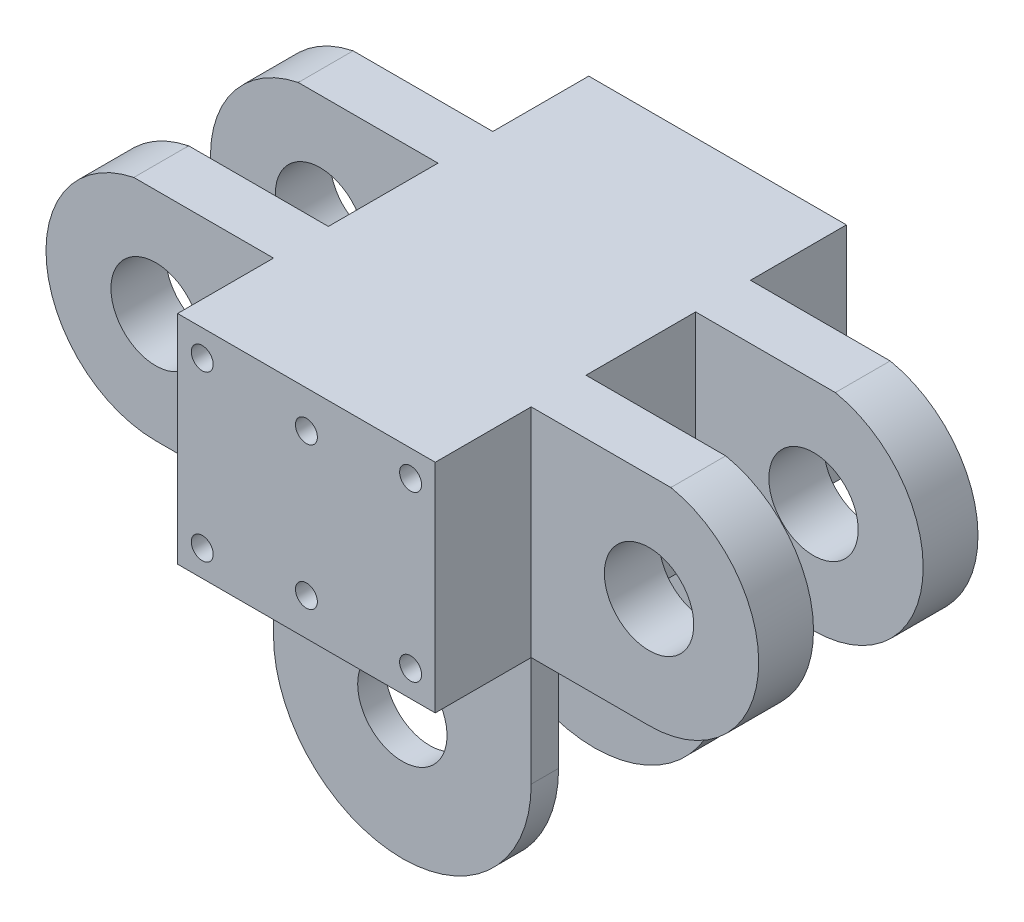
SolidWorks part; units mm, degrees
ref_plane "Płaszczyzna przednia" through (0, 0, 0) normal (0, 0, 1) x (1, 0, 0)
ref_plane "Płaszczyzna górna" through (0, 0, 0) normal (0, 1, 0) x (1, 0, 0)
ref_plane "Płaszczyzna prawa" through (0, 0, 0) normal (1, 0, 0) x (0, 0, -1)
sketch "Szkic1" plane through (0, 0, 0) normal (0, 0, 1) x (1, 0, 0)
  line L8 (47, 19.8) -> (0, 19.8) construction
  line L11 (0, 0) -> (47, 0)
  line L12 (0, 0) -> (0, 39.6)
  line L13 (0, 39.6) -> (47, 39.6)
  line L14 (47, 0) -> (47, 39.6)
  dimension "D1" = 39.6
  dimension "D4" = 47
extrude "Dodanie-wyciągnięcie3" add sketch "Szkic1" along normal blind 75
ref_plane "Płaszczyzna1" through (0, 0, 37.5) normal (0, 0, -1) x (-1, 0, 0)
ref_plane "Płaszczyzna2" through (0, 0, 27.5) normal (0, 0, -1) x (-1, 0, 0)
sketch "Szkic4" plane through (0, 0, 27.5) normal (0, 0, -1) x (-1, 0, 0)
  line L0 (-47, 39.6) -> (-72.4799, 39.6)
  line L2 (-68.5, 0) -> (-47, 0)
  line L3 (-47, 39.6) -> (0, 39.6) construction
  line L5 (-23.5, 39.6) -> (-23.5, 0) construction
  line L10 (-47, 39.6) -> (-47, 0)
  line L11 (-47, 0) -> (0, 0) construction
  line L12 (21.5, 0) -> (0, 0)
  line L13 (0, 39.6) -> (0, 0)
  line L14 (0, 39.6) -> (25.4799, 39.6)
  arc A4 (-72.4799, 39.6) -> (-68.5, 0) centre (-68.5, 20) ccw
  circle A5 centre (-68.5, 20) radius 8.15
  arc A6 (25.4799, 39.6) -> (21.5, 0) centre (21.5, 20) cw
  circle A7 centre (21.5, 20) radius 8.15
  dimension "D1" = 90
  dimension "D4" = 16.3
  dimension "D5" = 20
extrude "Dodanie-wyciągnięcie4" add sketch "Szkic4" along normal blind 10
mirror "Lustro1" about plane through (0, 0, 37.5) normal (0, 0, -1) of "Dodanie-wyciągnięcie4"
ref_plane "Płaszczyzna3" through (0, 0, 22.5) normal (0, 0, -1) x (-1, 0, 0)
sketch "Szkic5" plane through (0, 0, 22.5) normal (0, 0, -1) x (-1, 0, 0)
  line L0 (-47, 0) -> (0, 0)
  line L1 (0, 0) -> (0, -20)
  line L2 (-47, 0) -> (-47, -20)
  line L3 (-47, -20) -> (0, -20) construction
  arc A0 (-47, -20) -> (0, -20) centre (-23.5, -20) ccw
  circle A1 centre (-23.5, -20) radius 8.15
  dimension "D1" = 16.3
  dimension "D2" = 20
extrude "Dodanie-wyciągnięcie5" add sketch "Szkic5" along normal blind 5
mirror "Lustro2" about plane through (0, 0, 37.5) normal (0, 0, -1) of "Dodanie-wyciągnięcie5"
sketch "Szkic6" plane through (0, 0, 75) normal (0, 0, 1) x (1, 0, 0)
  line L0 (0, 19.8) -> (47, 19.8) construction
  line L1 (0, 39.6) -> (0, 0) construction
  line L2 (47, 39.6) -> (47, 0) construction
  line L3 (23.5, 34.8) -> (23.5, 4.8) construction
  line L4 (4.5, 4.8) -> (42.5, 4.8) construction
  line L5 (4.5, 4.8) -> (4.5, 34.8) construction
  line L6 (4.5, 34.8) -> (42.5, 34.8) construction
  line L7 (42.5, 4.8) -> (42.5, 34.8) construction
  line L8 (4.5, 4.8) -> (42.5, 34.8) construction
  line L9 (4.5, 34.8) -> (42.5, 4.8) construction
  circle A0 centre (4.5, 4.8) radius 2
  circle A1 centre (4.5, 34.8) radius 2
  circle A2 centre (42.5, 34.8) radius 2
  circle A3 centre (42.5, 4.8) radius 2
  circle A4 centre (23.5, 32.8) radius 2
  circle A5 centre (23.5, 6.8) radius 2
  point P6 (23.5, 19.8)
  dimension "D1" = 4
  dimension "D4" = 26
  dimension "D2" = 38
  dimension "D3" = 30
  dimension "D5" = 13
extrude "Wytnij-wyciągnięcie1" cut sketch "Szkic6" against normal blind 10
ref_point "Punkt1"
